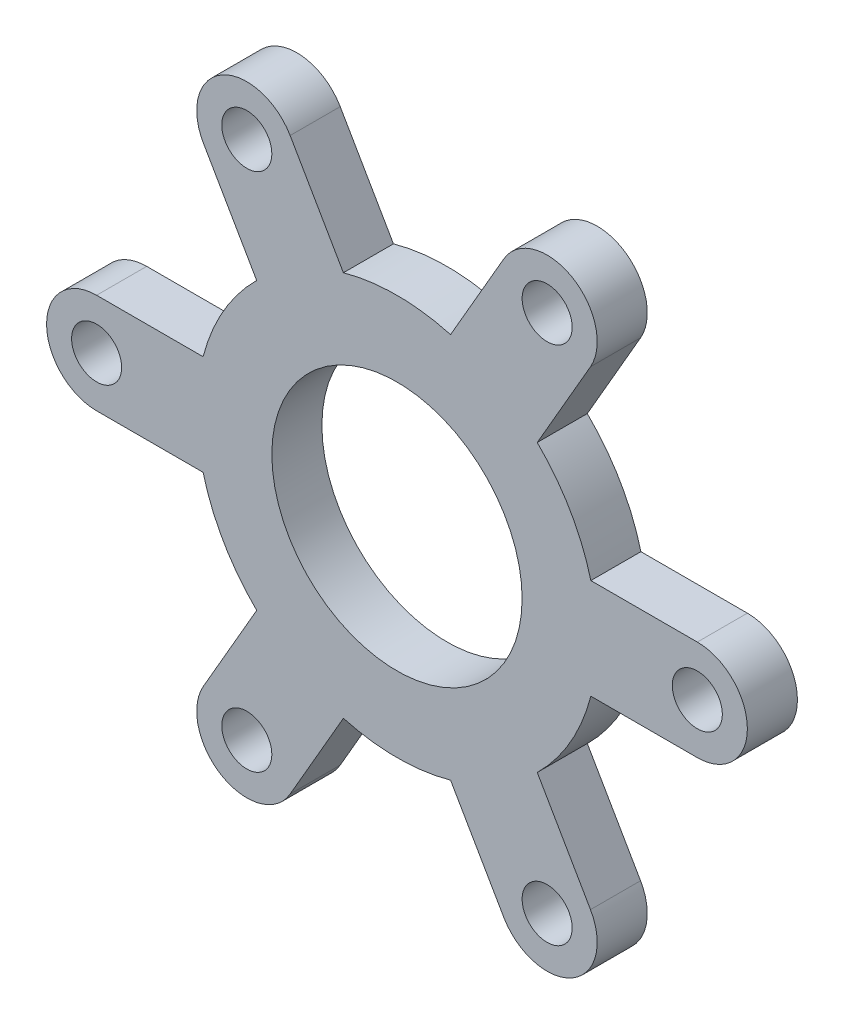
SolidWorks part; units mm, degrees
ref_plane "Front Plane" through (0, 0, 0) normal (0, 0, 1) x (1, 0, 0)
ref_plane "Top Plane" through (0, 0, 0) normal (0, 1, 0) x (1, 0, 0)
ref_plane "Right Plane" through (0, 0, 0) normal (1, 0, 0) x (0, 0, -1)
sketch "Sketch1" plane through (0, 0, 0) normal (0, 0, 1) x (1, 0, 0)
  line L0 (60, 10) -> (38.7298, 10)
  line L1 (60, -10) -> (38.7298, -10)
  line L2 (38.6603, -46.9615) -> (28.0252, -28.541)
  line L3 (21.3397, -56.9615) -> (10.7047, -38.541)
  line L4 (-21.3397, -56.9615) -> (-10.7047, -38.541)
  line L5 (-38.6603, -46.9615) -> (-28.0252, -28.541)
  line L6 (-60, -10) -> (-38.7298, -10)
  line L7 (-60, 10) -> (-38.7298, 10)
  line L8 (-38.6603, 46.9615) -> (-28.0252, 28.541)
  line L9 (-21.3397, 56.9615) -> (-10.7047, 38.541)
  line L10 (21.3397, 56.9615) -> (10.7047, 38.541)
  line L11 (38.6603, 46.9615) -> (28.0252, 28.541)
  arc A0 (-28.0252, 28.541) -> (-38.7298, 10) centre (0, 0) ccw
  circle A1 centre (0, 0) radius 60 construction
  circle A2 centre (60, 0) radius 5
  arc A3 (60, -10) -> (60, 10) centre (60, 0) ccw
  circle A4 centre (30, -51.9615) radius 5
  arc A5 (21.3397, -56.9615) -> (38.6603, -46.9615) centre (30, -51.9615) ccw
  circle A6 centre (-30, -51.9615) radius 5
  arc A7 (-38.6603, -46.9615) -> (-21.3397, -56.9615) centre (-30, -51.9615) ccw
  circle A8 centre (-60, 0) radius 5
  arc A9 (-60, 10) -> (-60, -10) centre (-60, 0) ccw
  circle A10 centre (-30, 51.9615) radius 5
  arc A11 (-21.3397, 56.9615) -> (-38.6603, 46.9615) centre (-30, 51.9615) ccw
  circle A12 centre (30, 51.9615) radius 5
  arc A13 (38.6603, 46.9615) -> (21.3397, 56.9615) centre (30, 51.9615) ccw
  arc A14 (-38.7298, -10) -> (-28.0252, -28.541) centre (0, 0) ccw
  arc A15 (-10.7047, -38.541) -> (10.7047, -38.541) centre (0, 0) ccw
  arc A16 (28.0252, -28.541) -> (38.7298, -10) centre (0, 0) ccw
  arc A17 (38.7298, 10) -> (28.0252, 28.541) centre (0, 0) ccw
  arc A18 (10.7047, 38.541) -> (-10.7047, 38.541) centre (0, 0) ccw
  circle A19 centre (0, 0) radius 25
  point P43 (0, 0)
  dimension "D1" = 120
  dimension "D2" = 80
  dimension "D3" = 20
  dimension "D4" = 10
  dimension "D6" = 50
  dimension "D5" = 6
extrude "Boss-Extrude1" add sketch "Sketch1" along normal blind 10
